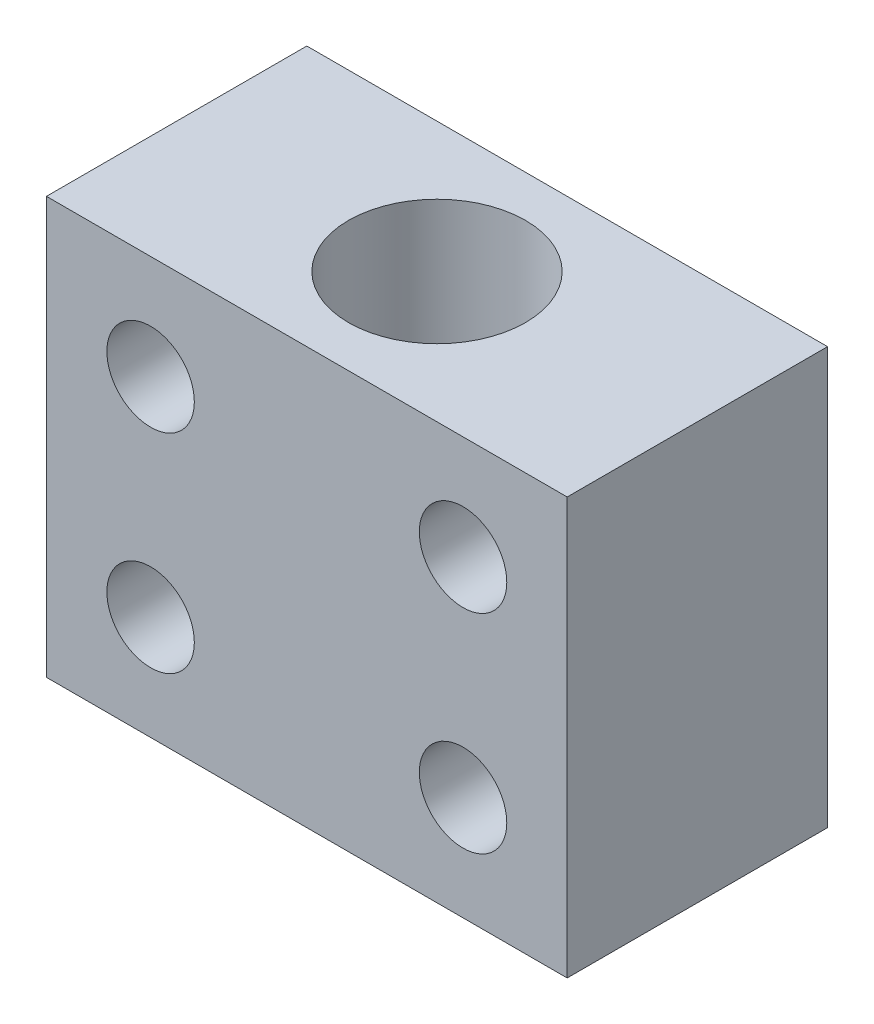
SolidWorks part; units mm, degrees
ref_plane "Alzado" through (0, 0, 0) normal (0, 0, 1) x (1, 0, 0)
ref_plane "Planta" through (0, 0, 0) normal (0, 1, 0) x (1, 0, 0)
ref_plane "Vista lateral" through (0, 0, 0) normal (1, 0, 0) x (0, 0, -1)
sketch "Croquis1" plane through (0, 0, 0) normal (0, 0, 1) x (1, 0, 0)
  line L1 (-25, -20) -> (25, -20)
  line L2 (-25, -20) -> (-25, 20)
  line L3 (-25, 20) -> (25, 20)
  line L4 (25, -20) -> (25, 20)
  line L5 (-25, -20) -> (25, 20) construction
  line L6 (-25, 20) -> (25, -20) construction
  point P0 (0, 0)
  dimension "D1" = 40
  dimension "D2" = 50
extrude "Saliente-Extruir1" add sketch "Croquis1" along normal mid plane 25
hole_wizard "Taladro de margen para M81" positions "Croquis2" profile "Croquis3" hole size "M8" standard "ISO" end condition through all
sketch "Croquis2" plane through (0, 0, 12.5) normal (0, 0, 1) x (1, 0, 0)
  line L1 (15, -10) -> (-15, -10) construction
  line L2 (15, -10) -> (15, 10) construction
  line L3 (15, 10) -> (-15, 10) construction
  line L4 (-15, -10) -> (-15, 10) construction
  line L5 (15, -10) -> (-15, 10) construction
  line L6 (15, 10) -> (-15, -10) construction
  point P0 (-15, 10)
  point P75 (-15, -10)
  point P78 (15, -10)
  point P81 (15, 10)
  point P83 (0, 0)
  dimension "D1" = 30
  dimension "D2" = 20
sketch "Croquis3" plane through (-15, 10, 12.5) normal (1, 0, 0) x (0, -1, 0)
  line L0 (0, 0) -> (0, 25)
  line L1 (0, 25) -> (4.2, 25)
  line L2 (4.2, 25) -> (4.2, 0)
  line L5 (4.2, 0) -> (0, 0)
  line L11 (0, -6.35) -> (0, 107.95) construction
  dimension "Diámetro de taladro hasta el siguiente" = 8.4
  dimension "Profundidad de taladro hasta el siguiente" = 25
hole_wizard "Taladro de margen para M161" positions "Croquis4" profile "Croquis5" hole size "M16" standard "ISO" end condition through all
sketch "Croquis4" plane through (0, 20, 0) normal (0, 1, 0) x (1, 0, 0)
  point P0 (0, 0)
sketch "Croquis5" plane through (0, 20, 0) normal (1, 0, 0) x (0, 0, 1)
  line L0 (0, 0) -> (0, 40)
  line L1 (0, 40) -> (8.5, 40)
  line L2 (8.5, 40) -> (8.5, 0)
  line L5 (8.5, 0) -> (0, 0)
  line L11 (0, -6.35) -> (0, 107.95) construction
  dimension "Diámetro de taladro hasta el siguiente" = 17
  dimension "Profundidad de taladro hasta el siguiente" = 40
